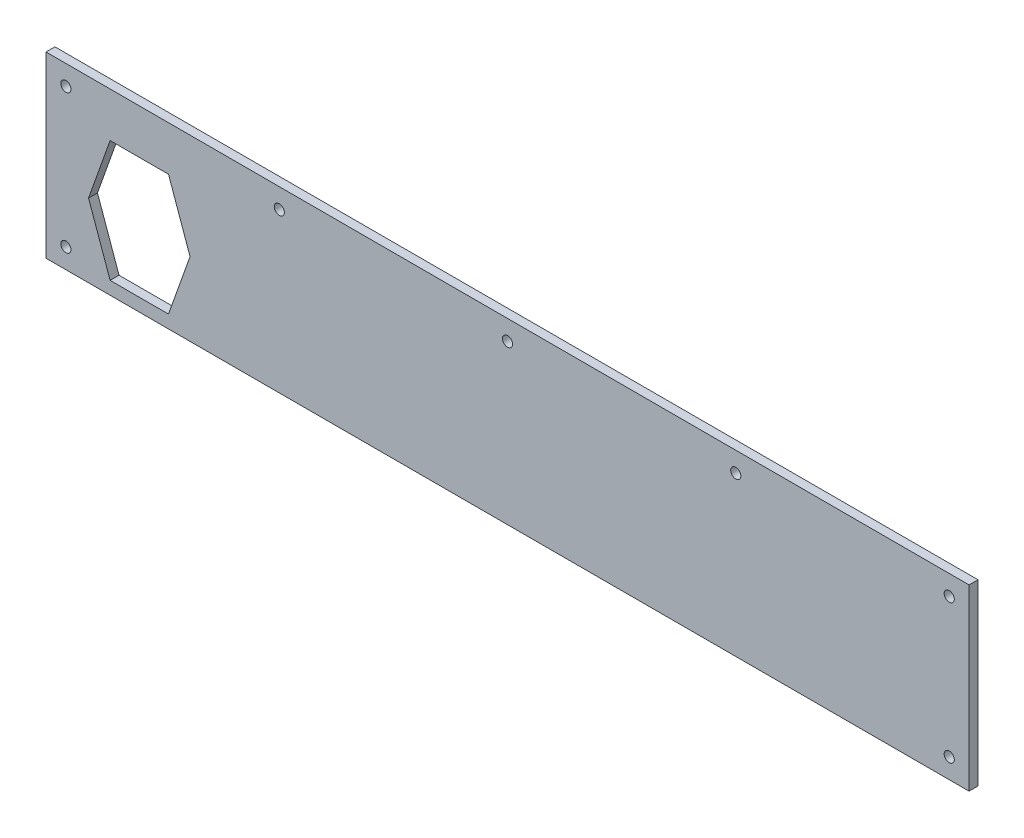
SolidWorks part; units mm, degrees
material "Acrylic (Medium-high impact)"
ref_plane "Front Plane" through (0, 0, 0) normal (0, 0, 1) x (1, 0, 0)
ref_plane "Top Plane" through (0, 0, 0) normal (0, 1, 0) x (1, 0, 0)
ref_plane "Right Plane" through (0, 0, 0) normal (1, 0, 0) x (0, 0, -1)
sketch "Sketch1" plane through (0, 0, 0) normal (0, 0, 1) x (1, 0, 0)
  line L0 (-222.5, 45) -> (-222.5, -45) construction
  line L1 (-232.5, -45) -> (232.5, -45)
  line L2 (-232.5, -45) -> (-232.5, 45)
  line L3 (-232.5, 45) -> (232.5, 45)
  line L4 (232.5, -45) -> (232.5, 45)
  line L5 (-232.5, -45) -> (232.5, 45) construction
  line L6 (-232.5, 45) -> (232.5, -45) construction
  line L7 (0, 45) -> (0, -45) construction
  line L8 (-232.5, 35) -> (2.55, 35) construction
  circle A0 centre (-222.5, 35) radius 2.55
  circle A1 centre (-222.5, -35) radius 2.55
  circle A2 centre (0, 35) radius 2.55
  circle A3 centre (-114.975, 35) radius 2.55
  circle A4 centre (222.5, -35) radius 2.55
  circle A5 centre (222.5, 35) radius 2.55
  circle A6 centre (114.975, 35) radius 2.55
  point P0 (0, 0)
  point P17 (-114.975, 35)
  dimension "D4" = 5.1
  dimension "D5" = 10
  dimension "D6" = 10
  dimension "D7" = 10
  dimension "D1" = 465
  dimension "D2" = 90
  dimension "D3" = 10
extrude "Boss-Extrude1" add sketch "Sketch1" along normal mid plane 4.4958
sketch "Sketch2" plane through (0, 0, 2.2479) normal (0, 0, 1) x (1, 0, 0)
  line L0 (-161, -8) -> (-171.5, 21.5) construction
  line L1 (-171.5, 21.5) -> (-199.5, 21.5) construction
  line L2 (-199.5, 21.5) -> (-210, -8) construction
  line L3 (-210, -8) -> (-199.5, -37.5) construction
  line L4 (-199.5, -37.5) -> (-171.5, -37.5) construction
  line L5 (-171.5, -37.5) -> (-161, -8) construction
  line L6 (-161, -8) -> (-171.5, 21.5) construction
  line L7 (-171.5, 21.5) -> (-199.5, 21.5) construction
  line L8 (-199.5, 21.5) -> (-210, -8) construction
  line L9 (-210, -8) -> (-199.5, -37.5) construction
  line L10 (-199.5, -37.5) -> (-171.5, -37.5) construction
  line L11 (-171.5, -37.5) -> (-161, -8) construction
  line L12 (-159.9385, -8) -> (-170.7945, 22.5)
  line L13 (-170.7945, 22.5) -> (-200.2055, 22.5)
  line L14 (-200.2055, 22.5) -> (-211.0615, -8)
  line L15 (-211.0615, -8) -> (-200.2055, -38.5)
  line L16 (-200.2055, -38.5) -> (-170.7945, -38.5)
  line L17 (-170.7945, -38.5) -> (-159.9385, -8)
  dimension "D1" = 1
extrude "Cut-Extrude1" cut sketch "Sketch2" against normal up to next
